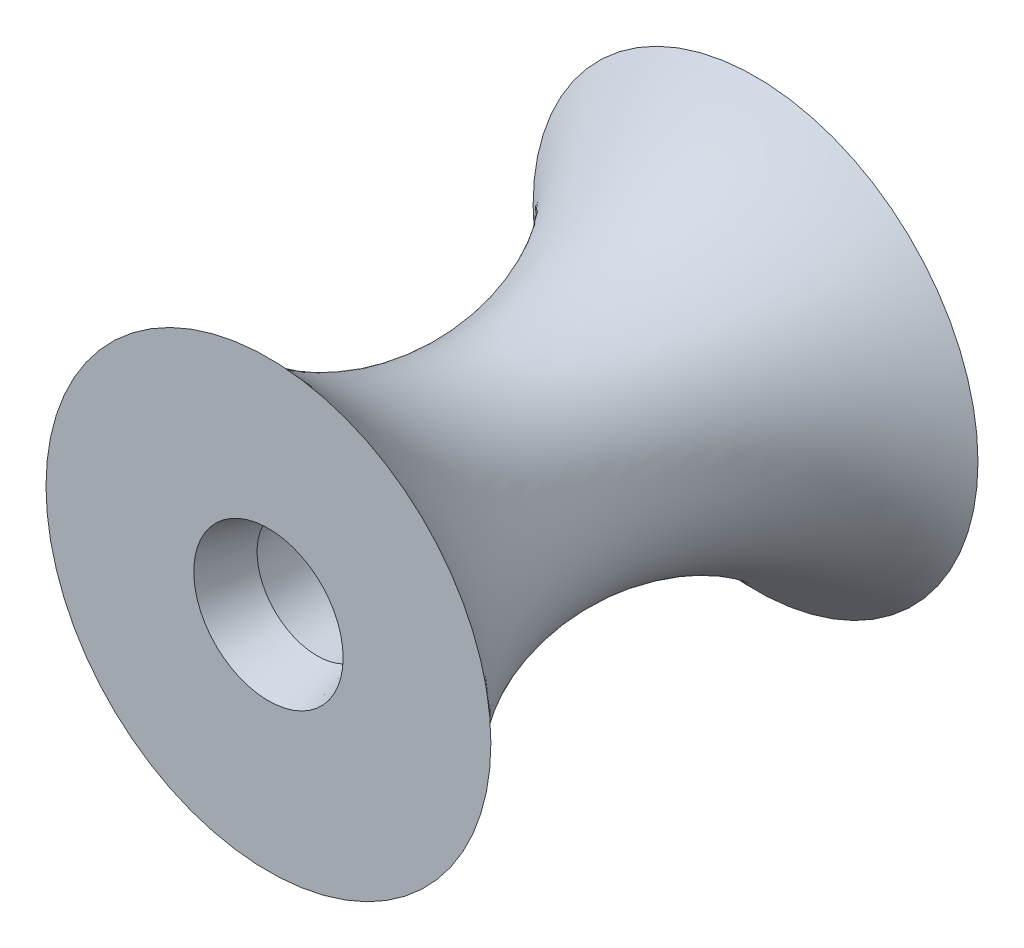
SolidWorks part; units mm, degrees
ref_plane "Front Plane" through (0, 0, 0) normal (0, 0, 1) x (1, 0, 0)
ref_plane "Top Plane" through (0, 0, 0) normal (0, 1, 0) x (1, 0, 0)
ref_plane "Right Plane" through (0, 0, 0) normal (1, 0, 0) x (0, 0, -1)
sketch "Sketch1" plane through (0, 0, 0) normal (0, 1, 0) x (1, 0, 0)
  line L0 (0, 0) -> (0, 8.3772) construction
  line L2 (-1.85, 13.5) -> (-1.85, 1.5)
  line L4 (-1.85, 13.5) -> (-2.3, 15)
  line L5 (-2.3, 15) -> (-6.85, 15)
  line L6 (-1.85, 1.5) -> (-2.3, 0)
  line L7 (-2.3, 0) -> (-6.85, 0)
  arc A0 (-6.85, 0) -> (-6.85, 15) centre (-13.1357, 7.5) ccw
  point P8 (-1.85, 7.8526)
  point P10 (-2.4139, 10.1272)
  point P11 (-3.3571, -4.898)
  point P12 (-1.85, -3.8251)
  point P14 (0, 0)
  point P15 (-2.3, -4.3522)
  point P16 (0, 0)
  point P17 (-3.35, 7.5)
  dimension "D1" = 1.85
  dimension "D2" = 15
  dimension "D3" = 5
  dimension "D4" = 2.3
  dimension "D5" = 1.5
  dimension "D6" = 1.5
revolve "Revolve1" add sketch "Sketch1" angle 360 about L0
